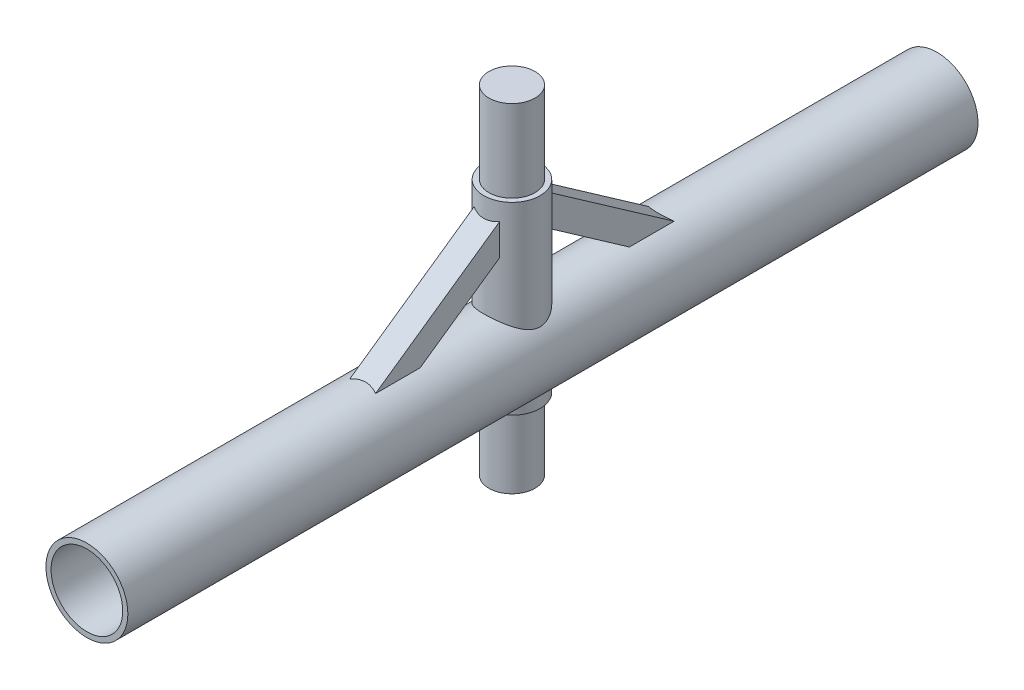
SolidWorks part; units mm, degrees
ref_plane "Front Plane" through (0, 0, 0) normal (0, 0, 1) x (1, 0, 0)
ref_plane "Top Plane" through (0, 0, 0) normal (0, 1, 0) x (1, 0, 0)
ref_plane "Right Plane" through (0, 0, 0) normal (1, 0, 0) x (0, 0, -1)
sketch "Sketch1" plane through (0, 0, 0) normal (0, 0, 1) x (1, 0, 0)
  circle A0 centre (0, 0) radius 40
  dimension "D1" = 80
extrude "Extrude-Thin1" add sketch "Sketch1" along normal mid plane 830 thin thin type one direction reverse wall 5
sketch "Sketch2" plane through (0, 0, 0) normal (0, 1, 0) x (1, 0, 0)
  circle A0 centre (0, 0) radius 22.5
  dimension "D1" = 45
extrude "Extrude-Thin3" add sketch "Sketch2" along normal blind 140 and the other way blind 40 thin
sketch "Sketch3" plane through (0, 140, 0) normal (0, 1, 0) x (1, 0, 0)
  circle A0 centre (0, 0) radius 22.5 construction
  circle A1 centre (0, 0) radius 22.5
extrude "Boss-Extrude1" add sketch "Sketch3" along normal blind 80 and the other way offset from surface (250 mm away) 70 other way up to face at (0, -40, 0)
sketch "Sketch4" plane through (0, 0, 0) normal (1, 0, 0) x (0, 0, -1)
  line L0 (0, 140) -> (-200, 0)
  point P2 (0, 0)
  point P3 (0, 0)
  dimension "D1" = 140
  dimension "D2" = 200
extrude "Extrude-Thin4" add sketch "Sketch4" along normal mid plane 25 separate body thin thin type one direction reverse wall 25
mirror "Mirror2" about plane through (0, 0, 0) normal (0, 0, 1) of bodies 105
sketch "Sketch5" plane through (0, 0, 415) normal (0, 0, 1) x (1, 0, 0)
  circle A1 centre (0, 0) radius 40
  circle A2 centre (0, 0) radius 40
  dimension "D1" = 0
sketch "Sketch6" plane through (0, 0, 415) normal (0, 0, 1) x (1, 0, 0)
  circle A0 centre (0, 0) radius 35 construction
  circle A1 centre (0, 0) radius 35
extrude "Cut-Extrude1" cut sketch "Sketch6" against normal through all
